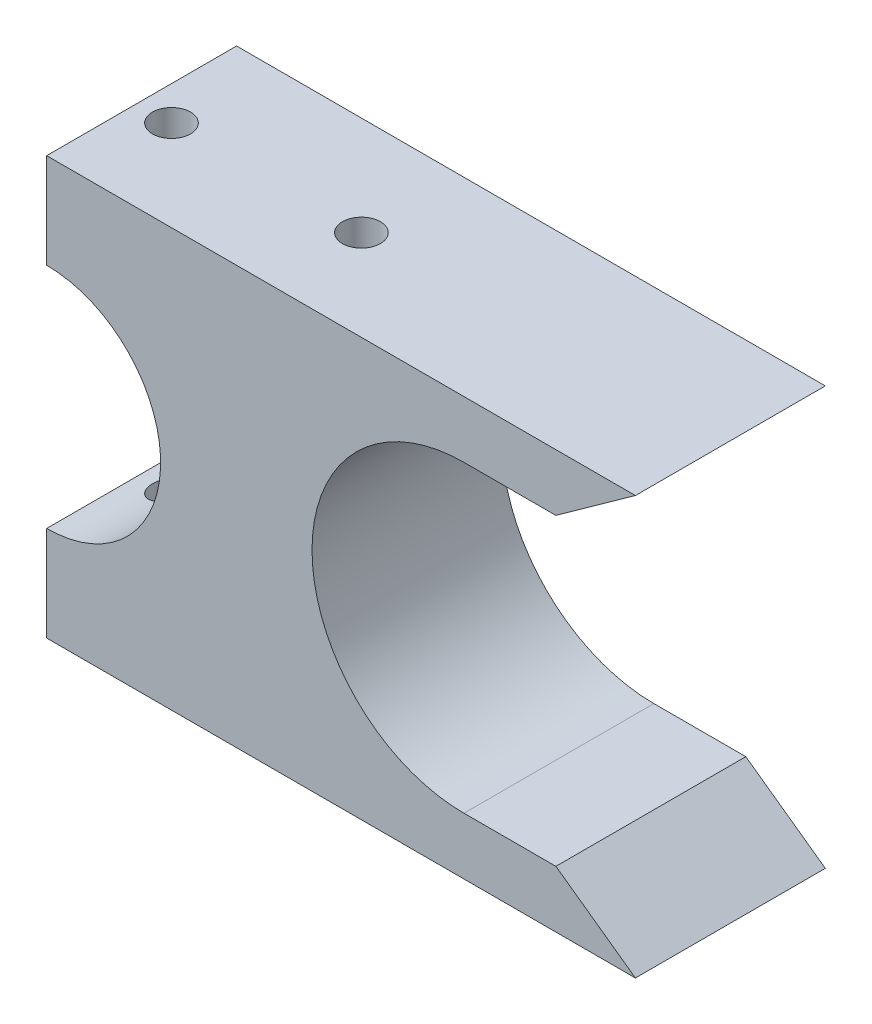
SolidWorks part; units mm, degrees
ref_plane "Front Plane" through (0, 0, 0) normal (0, 0, 1) x (1, 0, 0)
ref_plane "Top Plane" through (0, 0, 0) normal (0, 1, 0) x (1, 0, 0)
ref_plane "Right Plane" through (0, 0, 0) normal (1, 0, 0) x (0, 0, -1)
sketch "Sketch1" plane through (0, 0, 0) normal (0, 0, 1) x (1, 0, 0)
  line L0 (-13.9719, 11) -> (17.0281, 11)
  line L1 (17.0281, 11) -> (12.8419, 8)
  line L2 (-13.9719, 11) -> (-13.9719, 6)
  line L3 (12.8419, 8) -> (8, 8)
  line L4 (8, 0) -> (-13.9719, 0) construction
  line L5 (-13.9719, 0) -> (-13.9719, 6) construction
  line L6 (-7.9719, 0) -> (0, 0)
  arc A0 (8, 8) -> (0, 0) centre (8, 0) ccw
  arc A1 (-7.9719, 0) -> (-13.9719, 6) centre (-13.9719, 0) ccw
  point P5 (0, 0)
  dimension "D1" = 11
  dimension "D2" = 16
  dimension "D3" = 31
  dimension "D5" = 5
extrude "Boss-Extrude1" add sketch "Sketch1" along normal blind 10
mirror "Mirror1" about plane through (0, 0, 0) normal (0, 1, 0) of "Boss-Extrude1"
sketch "Sketch2" plane through (0, 11, 0) normal (0, 1, 0) x (1, 0, 0)
  line L0 (-13.9719, -5.2243) -> (-12.1745, -5.2243) construction
  line L1 (-13.9719, -10) -> (-13.9719, 0) construction
  line L2 (-12.1745, -5.2243) -> (-2.1745, -5.2243) construction
  circle A0 centre (-12.1745, -5.2243) radius 1
  circle A1 centre (-2.1745, -5.2243) radius 1
  dimension "D1" = 10
extrude "Cut-Extrude1" cut sketch "Sketch2" against normal through all
